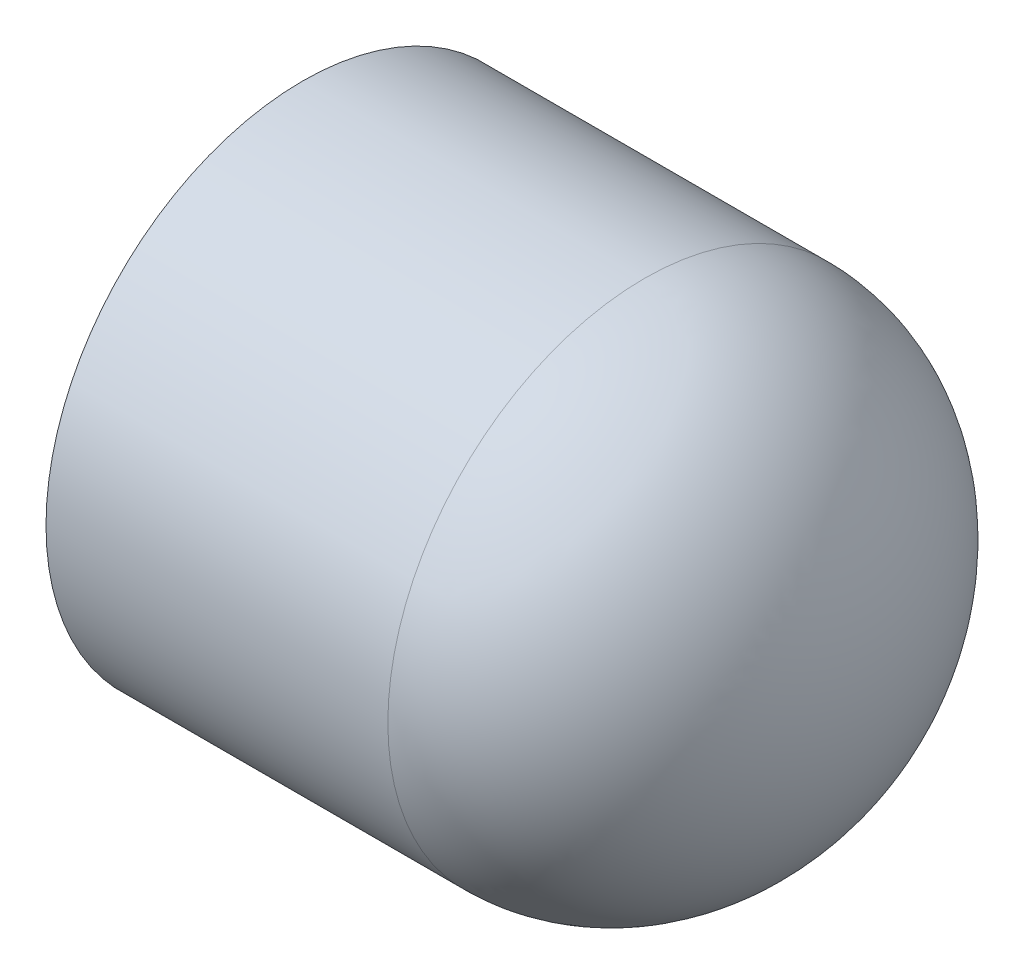
SolidWorks part; units mm, degrees
ref_plane "Front Plane" through (0, 0, 0) normal (0, 0, 1) x (1, 0, 0)
ref_plane "Top Plane" through (0, 0, 0) normal (0, 1, 0) x (1, 0, 0)
ref_plane "Right Plane" through (0, 0, 0) normal (1, 0, 0) x (0, 0, -1)
sketch "Sketch0" plane through (0, 0, 0) normal (0, 0, 1) x (1, 0, 0)
  line L3 (-14.7193, 0) -> (14.7193, 0) construction
  line L4 (-14.7193, 13.6144) -> (-14.7193, -13.6144) construction
  line L5 (3.4163, 10.6172) -> (-14.7193, 10.7696) construction
  line L6 (3.4163, 10.6172) -> (3.4163, -10.6172) construction
  line L7 (3.4163, -10.6172) -> (-14.7193, -10.7696) construction
  line L8 (-14.7193, 10.7696) -> (-14.7193, -10.7696) construction
  line L14 (3.4163, 7.8994) -> (3.4163, -7.8994) construction
  point P0 (3.4163, 0)
  dimension "H" = 11.303
  dimension "M" = 27.2288
  dimension "OD A" = 21.5392
  dimension "OD B" = 21.2344
  dimension "ID" = 15.7988
  dimension "L" = 29.4386
  dimension "C" = 18.1356
sketch "Sketch1" plane through (0, 0, 0) normal (0, 0, 1) x (1, 0, 0)
  line L1 (-14.7193, 0) -> (14.7193, 0) construction
  line L2 (-14.7193, 0) -> (14.7193, 0) construction
  line L3 (11.7221, 0) -> (14.7193, 0)
  line L4 (-14.7193, -13.6144) -> (-14.7193, -10.7696)
  line L5 (-14.7193, -10.7696) -> (3.4163, -10.6172)
  line L6 (3.4163, -10.6172) -> (3.4163, -13.6144) construction
  line L9 (3.4163, -13.6144) -> (-14.7193, -13.6144)
  ellipse E2 centre (3.4163, 0) end of major axis (3.4163, 13.6144) minor radius 11.303 (3.4163, -13.6144) -> (14.7193, 0) ccw
  ellipse E3 centre (3.4163, 0) end of major axis (3.4163, -10.6172) minor radius 8.3058 (3.4163, -10.6172) -> (11.7221, 0) ccw
revolve "Revolve1" add sketch "Sketch1" angle 360 about L1
